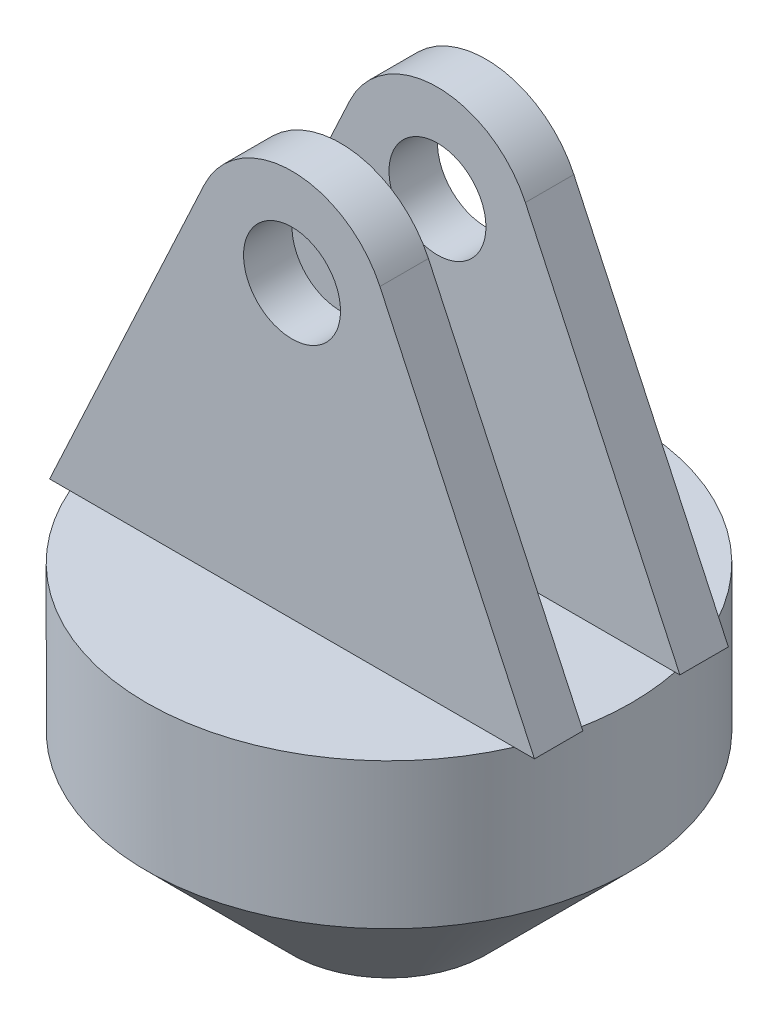
SolidWorks part; units mm, degrees
ref_plane "Plano frontal" through (0, 0, 0) normal (0, 0, 1) x (1, 0, 0)
ref_plane "Plano superior" through (0, 0, 0) normal (0, 1, 0) x (1, 0, 0)
ref_plane "Plano direito" through (0, 0, 0) normal (1, 0, 0) x (0, 0, -1)
sketch "Esboço1" plane through (0, 0, 0) normal (0, 0, 1) x (1, 0, 0)
  line L0 (0, 0) -> (0, 60)
  line L1 (0, 0) -> (74.6314, 0) construction
  line L2 (0, 0) -> (20, 0)
  line L3 (20, 0) -> (50, 30)
  line L4 (50, 30) -> (50, 60)
  line L5 (50, 60) -> (0, 60)
  dimension "D1" = 45
  dimension "D2" = 50
  dimension "D3" = 20
  dimension "D4" = 60
revolve "Revolução1" add sketch "Esboço1" angle 360 about L0
sketch "Esboço2" plane through (0, 0, 0) normal (0, 0, 1) x (1, 0, 0)
  line L0 (0, 0) -> (0, 201.8972) construction
  line L1 (50, 60) -> (18.1308, 128.4424)
  line L2 (50, 60) -> (-50, 60) construction
  line L3 (-50, 60) -> (-18.1308, 128.4424)
  line L4 (-50, 60) -> (50, 60)
  arc A0 (18.1308, 128.4424) -> (-18.1308, 128.4424) centre (0, 120) ccw
  circle A1 centre (0, 120) radius 10
  dimension "D1" = 40
  dimension "D3" = 20
  dimension "D2" = 60
extrude "Ressalto-extrusão1" add sketch "Esboço2" along normal blind 10 from offset 10
mirror "Espelhar1" about plane through (0, 0, 0) normal (0, 0, 1) of "Ressalto-extrusão1"
